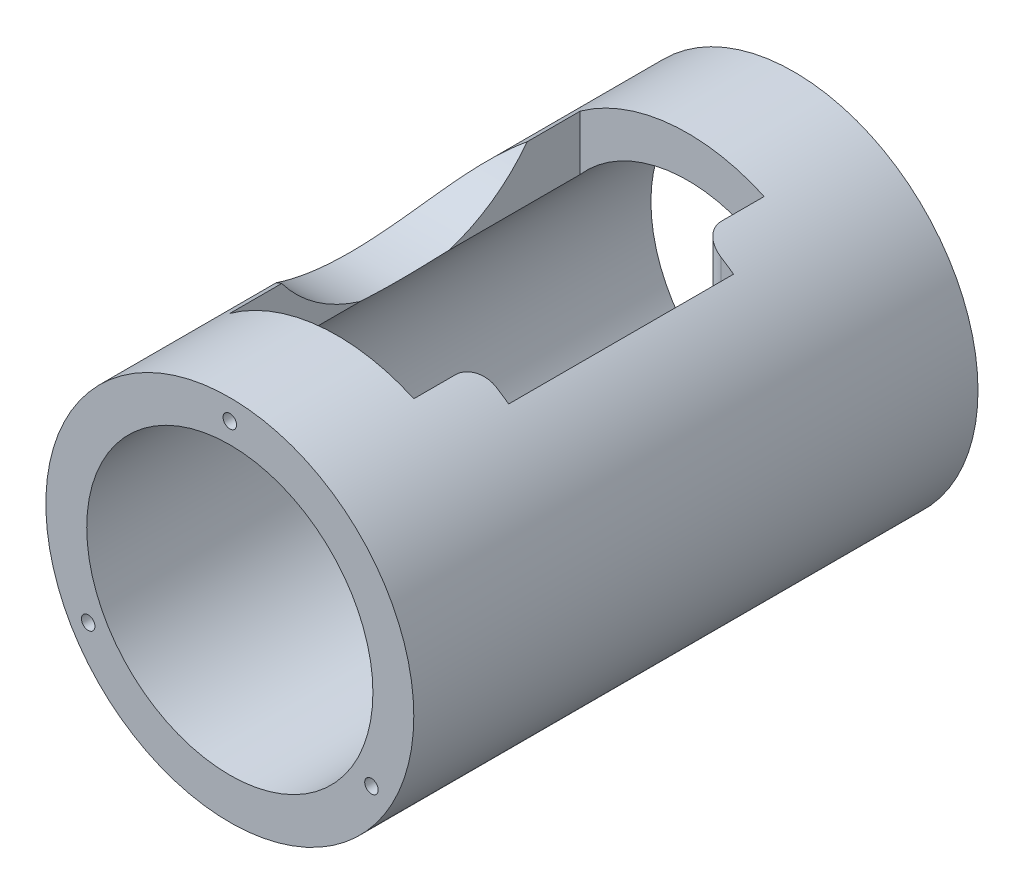
SolidWorks part; units mm, degrees
ref_plane "Alzado" through (0, 0, 0) normal (0, 0, 1) x (1, 0, 0)
ref_plane "Planta" through (0, 0, 0) normal (0, 1, 0) x (1, 0, 0)
ref_plane "Vista lateral" through (0, 0, 0) normal (1, 0, 0) x (0, 0, -1)
sketch "Croquis1" plane through (0, 0, 0) normal (0, 0, 1) x (1, 0, 0)
  circle A0 centre (0, 0) radius 45
  circle A1 centre (0, 0) radius 35
  dimension "D1" = 70
  dimension "D2" = 90
extrude "Saliente-Extruir1" add sketch "Croquis1" along normal mid plane 138
sketch "Croquis2" plane through (0, 0, 0) normal (0, 1, 0) x (1, 0, 0)
  line L0 (0, 80.6794) -> (0, -85.6158) construction
  line L1 (45, 69) -> (-45, 69) construction
  line L2 (-26.3, 43) -> (18.7, 43)
  line L3 (-26.3, 43) -> (-26.3, -42.7)
  line L4 (-26.3, -42.7) -> (18.7, -42.7)
  line L5 (18.7, 43) -> (18.7, 32.5)
  line L6 (-45, -69) -> (45, -69) construction
  line L7 (0, 0) -> (63.5667, 0) construction
  line L8 (23.7, 27.5) -> (26.7, 27.5)
  line L9 (26.7, 27.5) -> (26.7, -27.5)
  line L10 (26.7, -27.5) -> (23.7, -27.5)
  line L11 (18.7, -32.5) -> (18.7, -42.7)
  arc A0 (23.7, -27.5) -> (18.7, -32.5) centre (23.7, -32.5) ccw
  arc A1 (23.7, 27.5) -> (18.7, 32.5) centre (23.7, 32.5) cw
  point P19 (18.7, -27.5)
  dimension "D9" = 5
  dimension "D1" = 85.7
  dimension "D2" = 26
  dimension "D3" = 26.3
  dimension "D4" = 26.3
  dimension "D5" = 45
  dimension "D6" = 18.7
  dimension "D7" = 55
  dimension "D8" = 8
extrude "Cortar-Extruir1" cut sketch "Croquis2" along normal blind 138
sketch "Croquis3" plane through (0, 0, 0) normal (1, 0, 0) x (0, 0, -1)
  line L0 (0, 0) -> (0, 59) construction
  circle A0 centre (0, 59) radius 37.5
  dimension "D2" = 75
  dimension "D1" = 59
extrude "Cortar-Extruir2" cut sketch "Croquis3" against normal blind 138
sketch "Croquis4" plane through (0, 0, 69) normal (0, 0, 1) x (1, 0, 0)
  line L0 (0, 0) -> (0, 40) construction
  line L1 (0, 0) -> (34.641, -20) construction
  line L2 (0, 0) -> (-34.641, -20) construction
  circle A0 centre (0, 0) radius 40 construction
  dimension "D1" = 80
  dimension "D2" = 120
  dimension "D3" = 120
hole_wizard "Taladro roscado M41" positions "Croquis6" profile "Croquis5" tap size "M4" standard "DIN"
sketch "Croquis6" plane through (0, 0, 69) normal (0, 0, 1) x (1, 0, 0)
  point P0 (0, 40)
  point P1 (34.641, -20)
  point P4 (-34.641, -20)
sketch "Croquis5" plane through (0, 40, 69) normal (1, 0, 0) x (0, -1, 0)
  line L0 (0, 0) -> (0, 15.9914)
  line L1 (0, 15.9914) -> (1.65, 15)
  line L2 (1.65, 15) -> (1.65, 0)
  line L5 (1.65, 0) -> (0, 0)
  line L10 (0, 15.9914) -> (-1.65, 15) construction
  line L11 (0, -6.35) -> (0, 107.95) construction
  dimension "Diámetro de perforador para roscar" = 3.3
  dimension "Profundidad de perforador para roscar" = 15
  dimension "Ángulo de perforador" = 118
cosmetic thread "Rosca de taladro1" parameters "D1"=8, "D2"=4
cosmetic thread "Rosca de taladro2" parameters "D1"=8, "D2"=4
cosmetic thread "Rosca de taladro3" parameters "D1"=8, "D2"=4
mirror "Simetría1" about plane through (0, 0, 0) normal (0, 0, 1) of "Taladro roscado M41"
